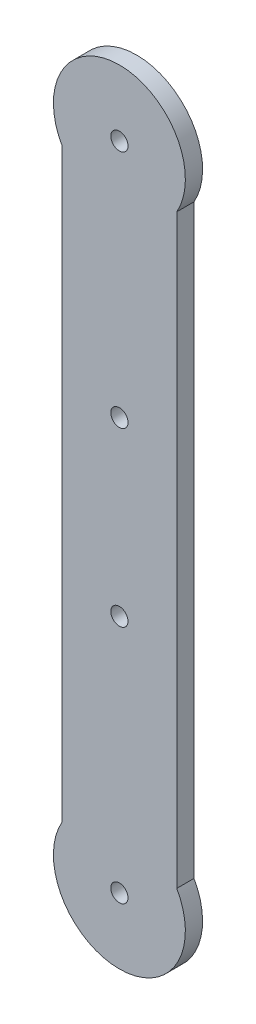
SolidWorks part; units mm, degrees
ref_plane "Alzado" through (0, 0, 0) normal (0, 0, 1) x (1, 0, 0)
ref_plane "Planta" through (0, 0, 0) normal (0, 1, 0) x (1, 0, 0)
ref_plane "Vista lateral" through (0, 0, 0) normal (1, 0, 0) x (0, 0, -1)
sketch "Croquis1" plane through (0, 0, 0) normal (0, 0, 1) x (1, 0, 0)
  line L0 (0, -56.75) -> (0, 56.75) construction
  line L2 (10, -56.75) -> (-10, -56.75)
  line L3 (10, -56.75) -> (10, 56.75)
  line L4 (10, 56.75) -> (-10, 56.75)
  line L5 (-10, -56.75) -> (-10, 56.75)
  line L6 (10, -56.75) -> (-10, 56.75) construction
  line L7 (10, 56.75) -> (-10, -56.75) construction
  circle A0 centre (0, 56.75) radius 11.5
  circle A1 centre (0, -56.75) radius 11.5
  point P4 (0, 0)
  point P7 (0, 45.25)
  point P8 (0, -68.25)
  point P9 (0, 0)
  dimension "D2" = 23
  dimension "D1" = 113.5
  dimension "D3" = 20
extrude "Saliente-Extruir1" add sketch "Croquis1" along normal blind 3 contours A1 L3 A0 L5 | L5 A0 L3 L4 | L3 A0 L5 L4 | L5 A1 L3 L2 | L3 A1 L5 L2
sketch "Croquis2" plane through (0, 0, 3) normal (0, 0, 1) x (1, 0, 0)
  circle A0 centre (0, 15) radius 1.5
  circle A1 centre (0, -15) radius 1.5
  circle A2 centre (0, 56.75) radius 1.5
  circle A3 centre (0, -56.75) radius 1.5
  dimension "D3" = 3
  dimension "D1" = 41.75
  dimension "D2" = 41.75
  dimension "D4" = 30
extrude "Cortar-Extruir1" cut sketch "Croquis2" against normal through all
